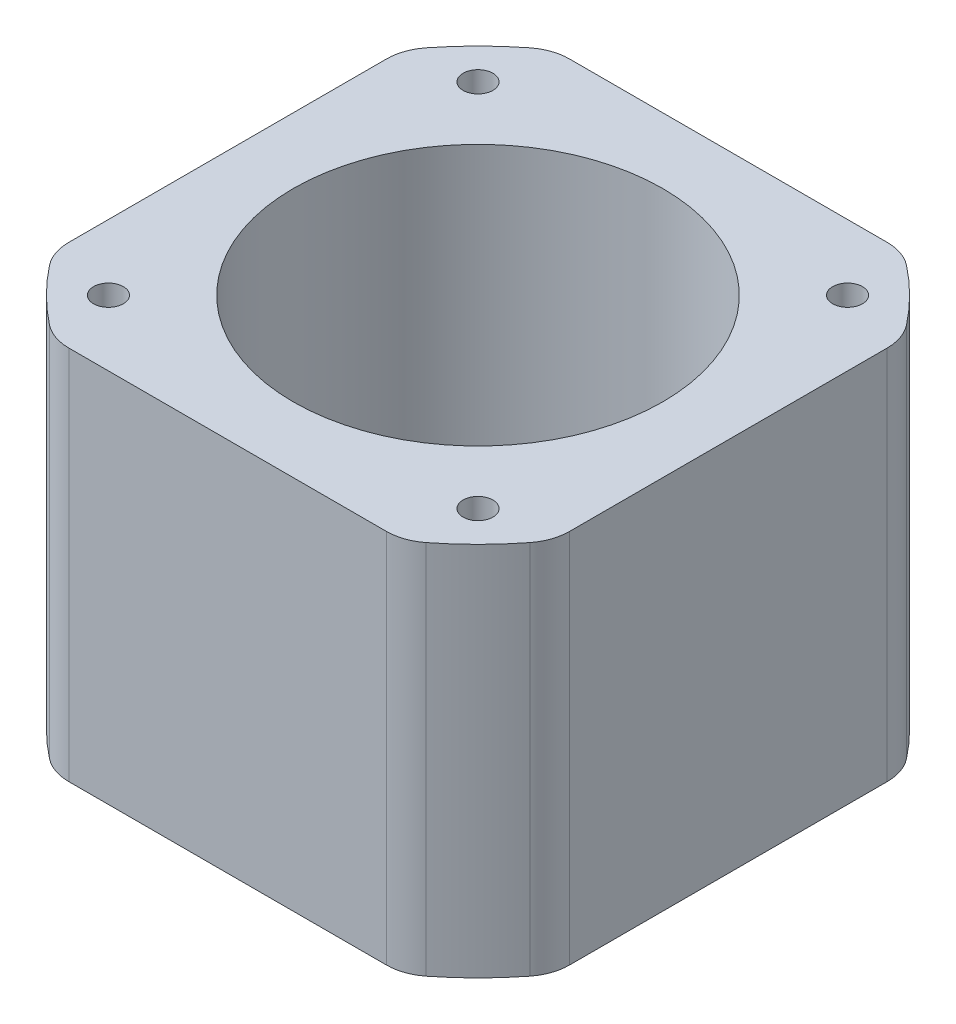
SolidWorks part; units mm, degrees
ref_plane "Спереди" through (0, 0, 0) normal (0, 0, 1) x (1, 0, 0)
ref_plane "Сверху" through (0, 0, 0) normal (0, 1, 0) x (1, 0, 0)
ref_plane "Справа" through (0, 0, 0) normal (1, 0, 0) x (0, 0, -1)
sketch "Эскиз1" plane through (0, 0, 0) normal (0, 1, 0) x (1, 0, 0)
  line L1 (-14.641, -21) -> (14.641, -21)
  line L2 (-21, -14.641) -> (-21, 14.641)
  line L3 (-14.641, 21) -> (14.641, 21)
  line L4 (21, -14.641) -> (21, 14.641)
  line L5 (-21, -21) -> (21, 21) construction
  line L6 (-21, 21) -> (21, -21) construction
  line L10 (-15.5, -15.5) -> (15.5, -15.5) construction
  line L11 (-15.5, -15.5) -> (-15.5, 15.5) construction
  line L12 (-15.5, 15.5) -> (15.5, 15.5) construction
  line L13 (15.5, -15.5) -> (15.5, 15.5) construction
  line L14 (-15.5, -15.5) -> (15.5, 15.5) construction
  line L15 (-15.5, 15.5) -> (15.5, -15.5) construction
  circle A0 centre (-15.5, 15.5) radius 1.25
  circle A1 centre (15.5, 15.5) radius 1.25
  circle A2 centre (15.5, -15.5) radius 1.25
  circle A3 centre (-15.5, -15.5) radius 1.25
  circle A4 centre (0, 0) radius 15.5
  arc A7 (-21, -14.641) -> (-14.641, -21) centre (0, 0) ccw
  arc A8 (-14.641, 21) -> (-21, 14.641) centre (0, 0) ccw
  arc A9 (21, 14.641) -> (14.641, 21) centre (0, 0) ccw
  arc A10 (14.641, -21) -> (21, -14.641) centre (0, 0) ccw
  point P0 (0, 0)
  point P13 (0, 0)
  dimension "D9" = 2.5
  dimension "D14" = 25.6
  dimension "D15" = 31
  dimension "D16" = 42
extrude "Бобышка-Вытянуть1" add sketch "Эскиз1" along normal blind 31.5
fillet "Скругление1" radius 4 8 edges at (-21, 15.75, -14.641) (-14.641, 15.75, -21) (14.641, 15.75, -21) (21, 15.75, -14.641) (21, 15.75, 14.641) (14.641, 15.75, 21) (-14.641, 15.75, 21) (-21, 15.75, 14.641)
